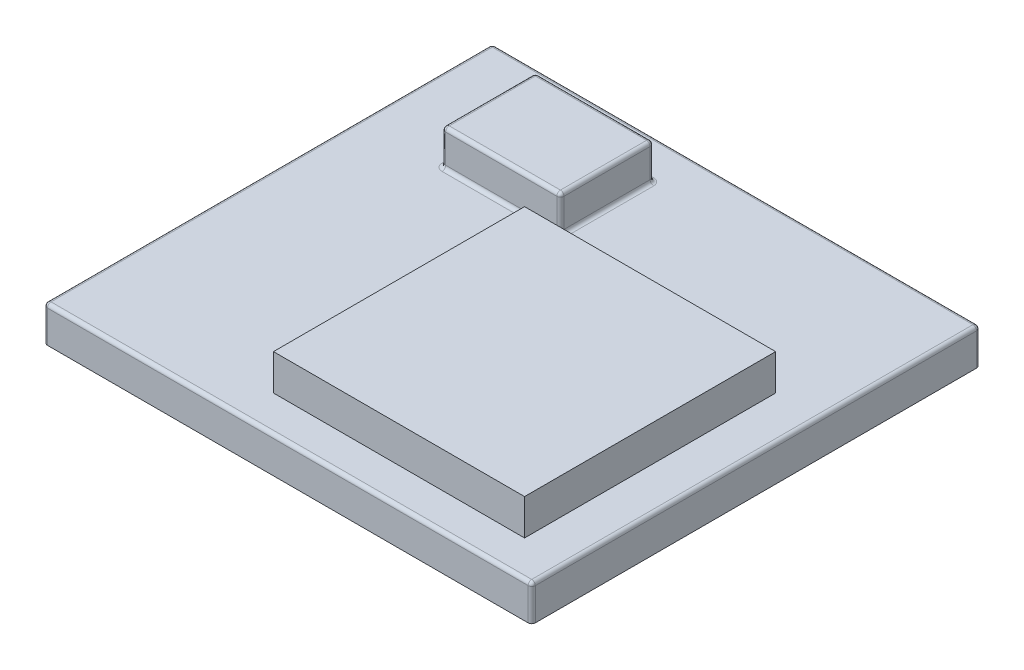
SolidWorks part; units mm, degrees
ref_plane "Front Plane" through (0, 0, 0) normal (0, 0, 1) x (1, 0, 0)
ref_plane "Top Plane" through (0, 0, 0) normal (0, 1, 0) x (1, 0, 0)
ref_plane "Right Plane" through (0, 0, 0) normal (1, 0, 0) x (0, 0, -1)
sketch "Sketch1" plane through (0, 0, 0) normal (0, 1, 0) x (1, 0, 0)
  line L0 (-6.8, -6.25) -> (6.8, 6.25) construction
  line L1 (-6.8, -6.25) -> (6.8, -6.25)
  line L2 (-6.8, -6.25) -> (-6.8, 6.25)
  line L3 (-6.8, 6.25) -> (6.8, 6.25)
  line L4 (6.8, -6.25) -> (6.8, 6.25)
  dimension "D1" = 12.5
  dimension "D2" = 13.6
extrude "Boss-Extrude1" add sketch "Sketch1" along normal blind 1
sketch "Sketch2" plane through (0, 1, 0) normal (0, 1, 0) x (1, 0, 0)
  line L0 (-6.8, -6.25) -> (6.8, -6.25) construction
  line L1 (-1.4, 1.75) -> (5.6, 1.75)
  line L2 (-1.4, 1.75) -> (-1.4, -5.25)
  line L3 (-1.4, -5.25) -> (5.6, -5.25)
  line L4 (5.6, 1.75) -> (5.6, -5.25)
  line L5 (6.8, -6.25) -> (6.8, 6.25) construction
  dimension "D1" = 7
  dimension "D2" = 1
  dimension "D3" = 1.2
extrude "Boss-Extrude2" add sketch "Sketch2" along normal blind 1
sketch "Sketch3" plane through (0, 1, 0) normal (0, 1, 0) x (1, 0, 0)
  line L0 (6.8, 6.25) -> (-6.8, 6.25) construction
  line L1 (-4.5, 5.15) -> (-1.2, 5.15)
  line L2 (-4.5, 5.15) -> (-4.5, 2.55)
  line L3 (-4.5, 2.55) -> (-1.2, 2.55)
  line L4 (-1.2, 5.15) -> (-1.2, 2.55)
  line L5 (-6.8, 6.25) -> (-6.8, -6.25) construction
  dimension "D1" = 3.3
  dimension "D2" = 2.6
  dimension "D3" = 1.1
  dimension "D4" = 2.3
extrude "Boss-Extrude3" add sketch "Sketch3" along normal blind 1
fillet "Fillet1" radius 0.1 20 edges at (-2.85, 1, -2.55) (-1.2, 1, -3.85) (-4.5, 1.5, -2.55) (-4.5, 1, -3.85) (-1.2, 1.5, -5.15) (-4.5, 1.5, -5.15) (-2.85, 1, -5.15) (-2.85, 2, -5.15) (-1.2, 2, -3.85) (-2.85, 2, -2.55) (-4.5, 2, -3.85) (6.8, 0.5, -6.25) (-6.8, 0.5, -6.25) (6.8, 0.5, 6.25) (-6.8, 0.5, 6.25) (-6.8, 1, 0) (0, 1, -6.25) (0, 1, 6.25) (6.8, 1, 0) (-1.2, 1.5, -2.55)
